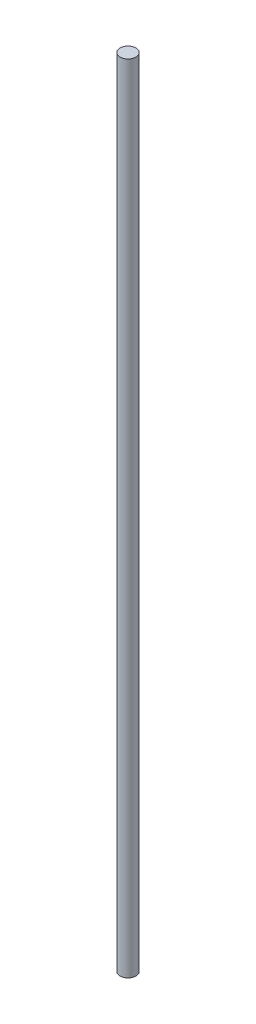
SolidWorks part; units mm, degrees
ref_plane "Front Plane" through (0, 0, 0) normal (0, 0, 1) x (1, 0, 0)
ref_plane "Top Plane" through (0, 0, 0) normal (0, 1, 0) x (1, 0, 0)
ref_plane "Right Plane" through (0, 0, 0) normal (1, 0, 0) x (0, 0, -1)
sketch "Sketch1" plane through (0, 0, 0) normal (0, 1, 0) x (1, 0, 0)
  circle A0 centre (-18.444, 5.194) radius 4
  dimension "D1" = 8
extrude "Boss-Extrude1" add sketch "Sketch1" along normal blind 400
